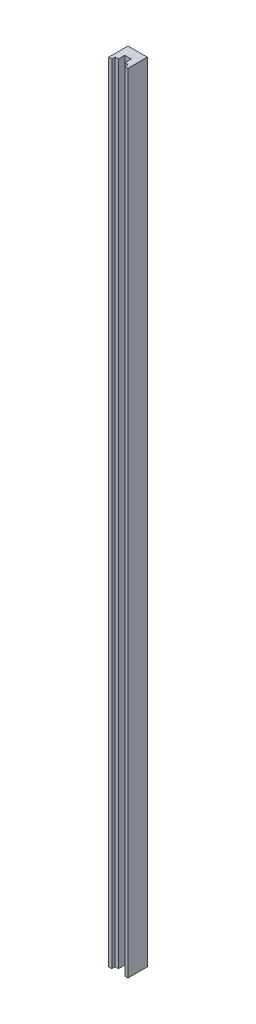
SolidWorks part; units mm, degrees
ref_plane "Front" through (0, 0, 0) normal (0, 0, 1) x (1, 0, 0)
ref_plane "Top" through (0, 0, 0) normal (0, 1, 0) x (1, 0, 0)
ref_plane "Right" through (0, 0, 0) normal (1, 0, 0) x (0, 0, -1)
sketch "Sketch1" plane through (0, 0, 0) normal (0, 1, 0) x (1, 0, 0)
  line L1 (15, -15) -> (-15, -15)
  line L2 (15, -15) -> (15, 15)
  line L3 (15, 15) -> (-15, 15)
  line L4 (-15, -15) -> (-15, 15)
  line L5 (15, -15) -> (-15, 15) construction
  line L6 (15, 15) -> (-15, -15) construction
  point P0 (0, 0)
  dimension "D1" = 30
  dimension "D2" = 30
extrude "Boss-Extrude1" add sketch "Sketch1" along normal blind 1225
sketch "Sketch2" plane through (0, 1225, 0) normal (0, 1, 0) x (1, 0, 0)
  line L0 (-15, -15) -> (15, -15) construction
  line L1 (-10, -15) -> (10, -15)
  line L2 (-10, -15) -> (-10, -10)
  line L3 (-10, -10) -> (10, -10)
  line L4 (10, -15) -> (10, -10)
  line L5 (-15, 15) -> (-15, -15) construction
  dimension "D1" = 20
  dimension "D2" = 5
  dimension "D3" = 5
extrude "Cut-Extrude1" cut sketch "Sketch2" against normal up to next
sketch "Sketch3" plane through (0, 1225, 0) normal (0, 1, 0) x (1, 0, 0)
  line L0 (10, -10) -> (-10, -10) construction
  line L1 (-5, -10) -> (5, -10)
  line L2 (-5, -10) -> (-5, 0)
  line L3 (-5, 0) -> (5, 0)
  line L4 (5, -10) -> (5, 0)
  line L5 (-10, -10) -> (-10, -15) construction
  dimension "D1" = 10
  dimension "D2" = 10
  dimension "D3" = 5
extrude "Cut-Extrude2" cut sketch "Sketch3" against normal up to next
sketch "Sketch4" plane through (-15, 0, 0) normal (-1, 0, 0) x (0, 0, 1)
  line L0 (-15, 1200) -> (15, 1200) construction
  line L1 (-15, 1225) -> (-15, 0) construction
  line L2 (15, 1225) -> (15, 0) construction
  line L3 (-15, 1000) -> (15, 1000) construction
  line L4 (-15, 800) -> (15, 800) construction
  line L5 (-15, 0) -> (15, 0) construction
  line L6 (-15, 700) -> (15, 700) construction
  dimension "D1" = 1200
  dimension "D2" = 1000
  dimension "D3" = 800
  dimension "D4" = 700
sketch "Sketch5" plane through (-15, 0, 0) normal (-1, 0, 0) x (0, 0, 1)
  line L0 (-15, 200) -> (15, 200) construction
  line L1 (-15, 1225) -> (-15, 0) construction
  line L2 (15, 1225) -> (15, 0) construction
  line L3 (-15, 0) -> (15, 0) construction
  dimension "D1" = 200
sketch "Sketch6" plane through (0, 0, -15) normal (0, 0, -1) x (-1, 0, 0)
  line L1 (-15, 1225) -> (-15, 0) construction
  line L2 (-15, 1225) -> (15, 1225) construction
  circle A0 centre (0, 1200) radius 4
  circle A1 centre (0, 1000) radius 4
  circle A2 centre (0, 800) radius 4
  circle A3 centre (0, 700) radius 4
  circle A4 centre (0, 650) radius 4
  circle A5 centre (0, 600) radius 4
  circle A6 centre (0, 550) radius 4
  circle A7 centre (0, 500) radius 4
  circle A8 centre (0, 450) radius 4
  circle A9 centre (0, 400) radius 4
  circle A10 centre (0, 350) radius 4
  circle A11 centre (0, 300) radius 4
  circle A12 centre (0, 250) radius 4
  circle A13 centre (0, 200) radius 4
  dimension "D1" = 8
  dimension "D2" = 25
  dimension "D3" = 15
  dimension "D4" = 200
  dimension "D5" = 200
  dimension "D6" = 100
  dimension "D7" = 50
  dimension "D8" = 50
  dimension "D9" = 50
  dimension "D10" = 50
  dimension "D11" = 50
  dimension "D12" = 50
  dimension "D13" = 50
  dimension "D14" = 50
  dimension "D15" = 50
  dimension "D16" = 50
extrude "Cut-Extrude3" cut sketch "Sketch6" against normal blind 3
hole_wizard "M6x1.0 Tapped Hole1" positions "Sketch8" profile "Sketch7" tap size "M6x1.0" standard "Ansi Metric"
sketch "Sketch8" plane through (0, 0, -15) normal (0, 0, -1) x (-1, 0, 0)
  line L0 (15, 1225) -> (15, 0) construction
  line L1 (-15, 0) -> (15, 0) construction
  point P0 (0, 75)
  point P1 (0, 25)
  dimension "D1" = 15
  dimension "D2" = 50
  dimension "D3" = 15
  dimension "D4" = 25
sketch "Sketch7" plane through (0, 75, -15) normal (1, 0, 0) x (0, 1, 0)
  line L0 (0, 0) -> (0, 16.5022)
  line L1 (0, 16.5022) -> (2.5, 15)
  line L2 (2.5, 15) -> (2.5, 0)
  line L5 (2.5, 0) -> (0, 0)
  line L10 (0, 16.5022) -> (-2.5, 15) construction
  line L11 (0, -6.35) -> (0, 107.95) construction
  dimension "Tap Drill Dia." = 5
  dimension "Tap Drill Depth" = 15
  dimension "Drill Angle" = 118
cosmetic thread "Hole Thread1" parameters "D1"=10, "D2"=6
cosmetic thread "Hole Thread2" parameters "D1"=10, "D2"=6
